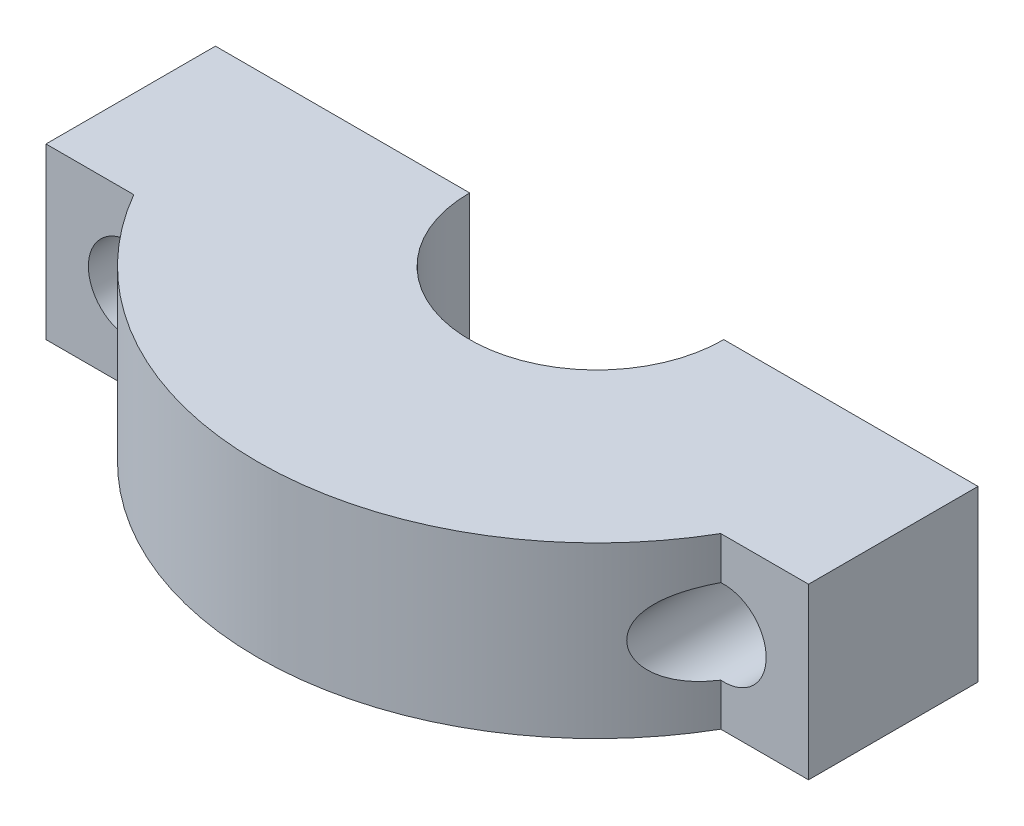
SolidWorks part; units mm, degrees
ref_plane "Front Plane" through (0, 0, 0) normal (0, 0, 1) x (1, 0, 0)
ref_plane "Top Plane" through (0, 0, 0) normal (0, 1, 0) x (1, 0, 0)
ref_plane "Right Plane" through (0, 0, 0) normal (1, 0, 0) x (0, 0, -1)
sketch "Sketch1" plane through (0, 0, 0) normal (0, 1, 0) x (1, 0, 0)
  line L0 (-45, 0) -> (45, 0)
  line L1 (-45, 0) -> (-45, -20)
  line L2 (-45, -20) -> (45, -20)
  line L3 (45, -20) -> (45, 0)
  circle A0 centre (0, 0) radius 15
  circle A1 centre (0, 0) radius 40
  point P7 (0, 0)
  dimension "D1" = 80
  dimension "D2" = 30
  dimension "D3" = 90
  dimension "D4" = 20
extrude "Boss-Extrude1" add sketch "Sketch1" along normal blind 20 contours A1 L0 L1 L2 | L2 A1 L0 A0 | L2 A1 | A1 L2 L3 L0
sketch "Sketch2" plane through (0, 0, 0) normal (0, 0, -1) x (-1, 0, 0)
  line L0 (0, 0) -> (0, 20) construction
  line L1 (-15, 0) -> (15, 0) construction
  line L2 (15, 20) -> (-15, 20) construction
  line L3 (0, 20) -> (0, 10) construction
  line L4 (0, 10) -> (-45, 10) construction
  line L5 (-45, 20) -> (-45, 0) construction
  circle A0 centre (-35, 10) radius 5
  circle A1 centre (35, 10) radius 5
  dimension "D1" = 10
  dimension "D2" = 70
extrude "Cut-Extrude1" cut sketch "Sketch2" against normal through all
